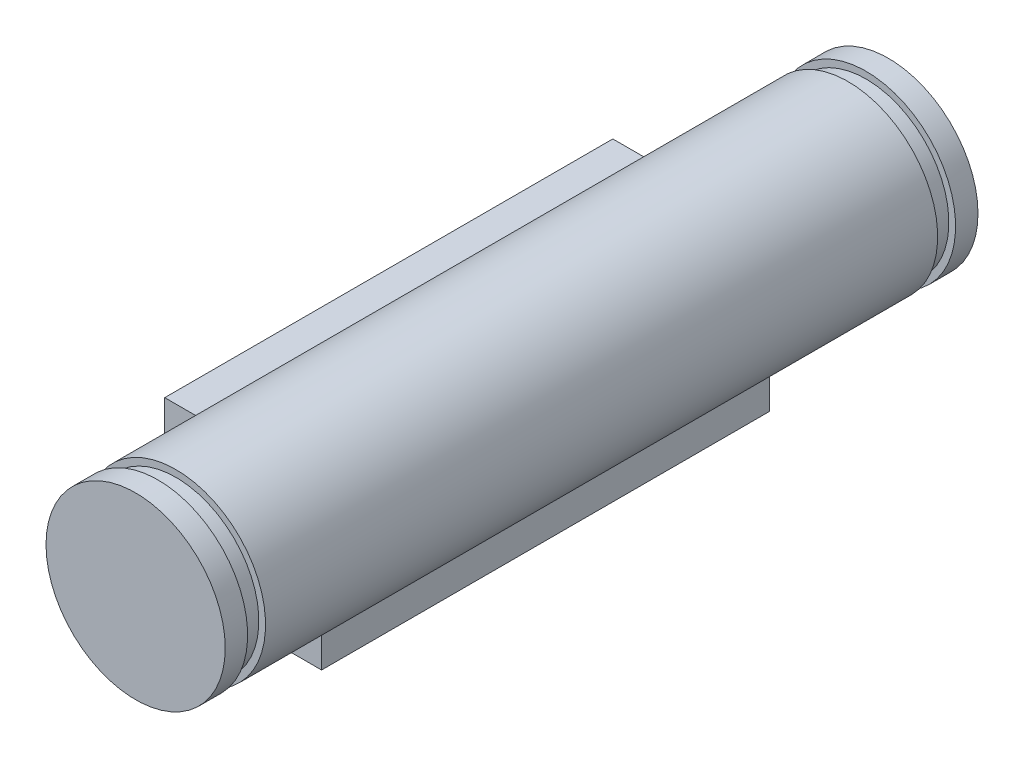
SolidWorks part; units mm, degrees
ref_plane "前视基准面" through (0, 0, 0) normal (0, 0, 1) x (1, 0, 0)
ref_plane "上视基准面" through (0, 0, 0) normal (0, 1, 0) x (1, 0, 0)
ref_plane "右视基准面" through (0, 0, 0) normal (1, 0, 0) x (0, 0, -1)
sketch "草图1" plane through (0, 0, 0) normal (0, 0, 1) x (1, 0, 0)
  line L0 (0, 7.5) -> (0, -7.5) construction
  line L1 (-7.5, -7.5) -> (7.5, -7.5)
  line L2 (-7.5, 7.5) -> (-7.5, -7.5)
  line L3 (-7.5, 7.5) -> (7.5, 7.5)
  line L4 (7.5, -7.5) -> (7.5, 7.5)
  line L5 (7.5, 0) -> (-7.5, 0) construction
  circle A0 centre (0, 0) radius 4
  circle A1 centre (-5, 5) radius 1.5
  circle A2 centre (-5, -5) radius 1.5
  circle A3 centre (5, -5) radius 1.5
  circle A4 centre (5, 5) radius 1.5
extrude "凸台-拉伸1" add sketch "草图1" along normal mid plane 33.6 contours A0
sketch "草图2" plane through (0, 0, 0) normal (1, 0, 0) x (0, 0, -1)
  line L0 (18.8, 0) -> (14.4802, 0) construction
  line L1 (-15, 3.7) -> (-15.8, 3.7)
  line L2 (-15, 4) -> (-15, 3.7)
  line L3 (-15.8, 3.7) -> (-15.8, 4)
  line L4 (-15.8, 4) -> (-15, 4)
  line L5 (0, 0) -> (0, 3) construction
  line L7 (15.8, 4) -> (15, 4)
  line L8 (15.8, 3.7) -> (15.8, 4)
  line L9 (15, 4) -> (15, 3.7)
  line L14 (15, 3.7) -> (15.8, 3.7)
revolve "切除-旋转1" cut sketch "草图2" angle 360 about L0
sketch "草图3" plane through (0, 0, 0) normal (0, 0, 1) x (-1, 0, 0)
  line L18 (5.5, 1.5) -> (3.7081, 1.5)
  line L19 (5.5, -1.53) -> (5.5, 1.5)
  line L20 (3.6958, -1.53) -> (5.5, -1.53)
  line L21 (-1.5, 5.5) -> (-1.5, 3.7081)
  line L22 (1.53, 5.5) -> (-1.5, 5.5)
  line L23 (1.53, 3.6958) -> (1.53, 5.5)
  arc A8 (3.7081, 1.5) -> (1.53, 3.6958) centre (0, 0) ccw
  arc A9 (-1.5, 3.7081) -> (3.6958, -1.53) centre (0, 0) ccw
extrude "凸台-拉伸2" add sketch "草图3" along normal mid plane 20
sketch "草图4" plane through (0, 0, -16.8) normal (0, 0, -1) x (-1, 0, 0)
  line L0 (1, -1.118) -> (1, 1.118)
  arc A0 (1, 1.118) -> (1, -1.118) centre (0, 0) ccw
extrude "切除-拉伸1" cut sketch "草图4" against normal blind 20
